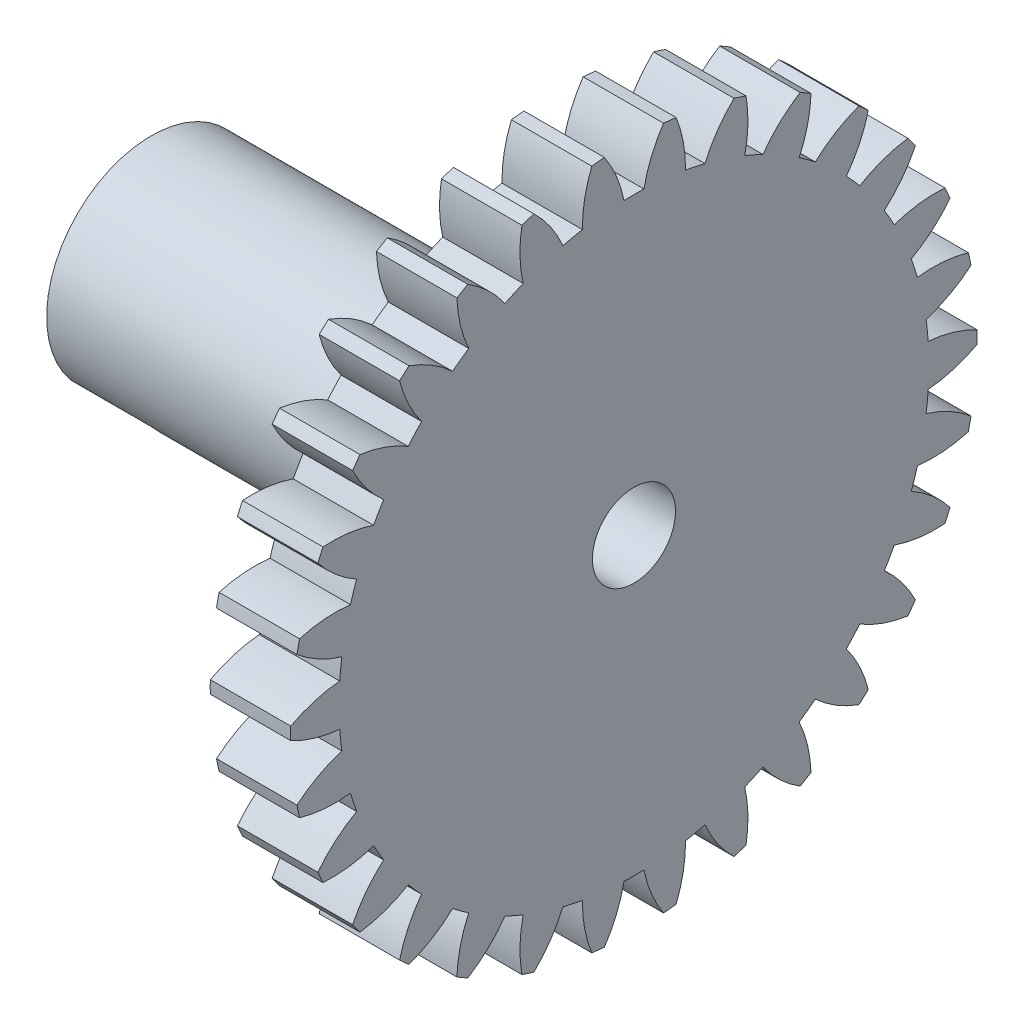
SolidWorks part; units mm, degrees
ref_plane "Plane1" through (0, 0, 0) normal (0, 0, 1) x (1, 0, 0)
ref_plane "Plane2" through (0, 0, 0) normal (0, 1, 0) x (1, 0, 0)
ref_plane "Plane3" through (0, 0, 0) normal (1, 0, 0) x (0, 0, -1)
other "Configuration Table"
sketch "HoldingSke" plane through (0, 0, 0) normal (0, 1, 0) x (1, 0, 0)
  line L0 (0, 0) -> (1.0825, -0.625)
  line L1 (-15, 0) -> (100, 0) construction
  line L2 (0, 0) -> (-2.1039, 2.3779)
  line L3 (0, 0) -> (-11.863, 4.5341)
  line L4 (0, 0) -> (7.479, 4.318)
  line L5 (0, 0) -> (-10.3065, -3.844)
  line L6 (0, 0) -> (-4.5593, -3.0762)
  line L7 (-2.1039, 2.3779) -> (0.2639, 13.1201)
  line L8 (-76.2, 54.61) -> (-76.1, 54.61)
  line L9 (-71.009, 38.7566) -> (-53.1078, 45.2721)
  line L10 (-76.2, 71.12) -> (104.1128, 71.12)
  line L11 (0, 0) -> (-5.5, 0)
  line L12 (-76.2, 101.6) -> (-76.17, 101.6)
  line L13 (24.9733, 27.94) -> (52.9518, 28.4284)
  line L14 (24.9733, 27.94) -> (24.9743, 27.94)
  line L15 (24.9733, 27.94) -> (100.4006, 29.5858)
  line L16 (-63.627, -0.8) -> (-12.827, -0.8)
  circle A0 centre (0, 0) radius 0.4
  circle A1 centre (0, 0) radius 1.9
  circle A2 centre (0, 0) radius 1.9
  circle A3 centre (0, 0) radius 0.4
  dimension "MHD" = 3.8
  dimension "Hub_dia" = 3.8
  dimension "Bore" = 0.8
  dimension "MBD" = 0.8
  dimension "Num_teeth" = 30
  dimension "Pitch" = 1.25
  dimension "Overall_len" = 11
  dimension "Show_teeth" = 30
  dimension "Thickness" = 5.5
  dimension "OAL" = 11.0001
  dimension "T_dim" = 0.1
  dimension "Ap" = 20
  dimension "H" = 19.05
  dimension "Pitch_radius" = 180.3128
  dimension "Width" = 5.5
  dimension "Backlash" = 0.03
  dimension "Addendum_fac" = 1
  dimension "Dedendum_fac" = 1.25
  dimension "Clearance_fac" = 0.25
  dimension "Dedendum_add" = 0.001
  dimension "Module" = 0.8
sketch "BasProSke" plane through (0, 0, 0) normal (0, 1, 0) x (1, 0, 0)
  line L0 (-10, 0) -> (60, 0) construction
  line L1 (0, 0) -> (0, 12.8)
  line L2 (0, 0) -> (5.5, 0)
  line L3 (5.5, 0) -> (5.5, 12.8)
  line L4 (5.5, 12.8) -> (0, 12.8)
  dimension "Thickness" = 5.5
  dimension "Diameter" = 25.6
revolve "Base-Revolve" add sketch "BasProSke" angle 360 about L0
sketch "TooCutSke" plane through (0, 0, 0) normal (1, 0, 0) x (0, 0, -1)
  line L1 (0, 0) -> (0, 107) construction
  line L2 (0, 0) -> (-0.6805, 11.9807) construction
  line L3 (0, 0) -> (-2.5058, 23.8411) construction
  line L4 (-0.6805, 11.9807) -> (-1.2529, 11.9205) construction
  arc A0 (0.3724, 10.9927) -> (-0.3724, 10.9927) centre (0, 0) ccw
  arc A1 (1.1205, 12.7764) -> (-1.1205, 12.7764) centre (0, 0) ccw
  circle A2 centre (0, 0) radius 12 construction
  circle A3 centre (0, 0) radius 11.2763 construction
  arc A4 (-0.3724, 10.9927) -> (-1.1205, 12.7764) centre (-5.0822, 10.0661) ccw
  arc A5 (1.1205, 12.7764) -> (0.3724, 10.9927) centre (5.0822, 10.0661) ccw
  dimension "Root_dia" = 21.998
  dimension "Overcut_dia" = 25.6508
  dimension "Pitch_dia" = 24
  dimension "Base_dia" = 22.5526
  dimension "Flank_rad" = 4.8
  dimension "Half_ang" = 6
  dimension "Half_CT" = 0.5755
extrude "ToothCut" cut sketch "TooCutSke" along normal through all
fillet "Breaks" [suppressed] radius 0.016
fillet "RootFillets" [suppressed] radius 0.201
pattern_circular "TeethCuts" count 30 over 360 about axis through (0, 0, 0) along (1, 0, 0) of "ToothCut", "RootFillets", "Breaks"
sketch "HubNeaOneSke" plane through (0, 0, 0) normal (-1, 0, 0) x (0, 0, 1)
  circle A0 centre (0, 0) radius 1.9
  dimension "Diameter" = 3.8
extrude "HubNearOne" add sketch "HubNeaOneSke" along normal blind 5.5001
sketch "HubNeaBotSke" plane through (0, 0, 0) normal (-1, 0, 0) x (0, 0, 1)
  circle A0 centre (0, 0) radius 1.9
  dimension "Diameter" = 3.8
extrude "HubNearBoth" [suppressed] add sketch "HubNeaBotSke" along normal blind 2.75
ref_plane "FarPln" through (5.5, 0, 0) normal (1, 0, 0) x (0, 0, -1)
sketch "HubFarSke" plane through (5.5, 0, 0) normal (1, 0, 0) x (0, 0, -1)
  circle A0 centre (0, 0) radius 1.9
  dimension "Diameter" = 3.8
extrude "HubFar" [suppressed] add sketch "HubFarSke" along normal blind 2.75
sketch "BorSke" plane through (0, 0, 0) normal (1, 0, 0) x (0, 0, -1)
  circle A0 centre (0, 0) radius 0.4
  dimension "Diameter" = 0.8
extrude "Bore" cut sketch "BorSke" along normal mid plane 22.0001
sketch "KeySke" plane through (0, 0, 0) normal (1, 0, 0) x (0, 0, -1)
  line L0 (-0.05, 0) -> (-0.05, 0.5)
  line L1 (-0.05, 0.5) -> (0.05, 0.5)
  line L2 (0.05, 0.5) -> (0.05, 0)
  line L3 (0, 0) -> (0, 34) construction
  line L4 (-0.05, 0) -> (0.05, 0)
  dimension "Offset" = 0.5
  dimension "Width" = 0.1
extrude "Keyway" [suppressed] cut sketch "KeySke" along normal mid plane 22.0001
pattern_circular "Keyway2" [suppressed] count 2 every 90 about axis through (-10, 0, 0) along (1, 0, 0)
sketch "Sketch1" plane through (0, 0, 0) normal (-1, 0, 0) x (0, 0, 1)
  circle A0 centre (0, 0) radius 3.9
  dimension "D1" = 7.8
extrude "Boss-Extrude1" add sketch "Sketch1" along normal blind 15
sketch "Sketch2" plane through (-15, 0, 0) normal (-1, 0, 0) x (0, 0, 1)
  circle A0 centre (0, 0) radius 1.55
  dimension "D1" = 3.1
extrude "Cut-Extrude1" cut sketch "Sketch2" against normal blind 28
sketch "Sketch3" plane through (-15, 0, 0) normal (-1, 0, 0) x (0, 0, 1)
  line L0 (-3, -2.492) -> (3, -2.492)
  circle A1 centre (0, 0) radius 3.9
  arc A2 (-3, -2.492) -> (3, -2.492) centre (0, 0) ccw
  dimension "D2" = 6
  dimension "D1" = 0
extrude "Cut-Extrude2" cut sketch "Sketch3" against normal blind 3
sketch "Sketch4" plane through (5.5, 0, 0) normal (1, 0, 0) x (0, 0, -1)
  arc A120 (-12.7978, -0.2349) -> (-10.9714, -0.7787) centre (-10.5422, 4.0021) ccw
  arc A121 (-10.9714, -0.7787) -> (-10.8935, -1.5194) centre (0, 0) ccw
  arc A122 (-10.8935, -1.5194) -> (-12.567, -2.4311) centre (-9.4798, -6.1065) ccw
  arc A123 (-12.567, -2.4311) -> (-12.4693, -2.8906) centre (0, 0) ccw
  arc A124 (-12.4693, -2.8906) -> (-10.5698, -3.0427) centre (-11.1439, 1.7228) ccw
  arc A125 (-10.5698, -3.0427) -> (-10.3396, -3.7511) centre (0, 0) ccw
  arc A126 (-10.3396, -3.7511) -> (-11.7869, -4.9908) centre (-8.003, -7.944) ccw
  arc A127 (-11.7869, -4.9908) -> (-11.5959, -5.4199) centre (0, 0) ccw
  arc A128 (-11.5959, -5.4199) -> (-9.7062, -5.1738) centre (-11.2586, -0.6318) ccw
  arc A129 (-9.7062, -5.1738) -> (-9.3337, -5.8189) centre (0, 0) ccw
  arc A130 (-9.3337, -5.8189) -> (-10.4917, -7.3324) centre (-6.1764, -9.4343) ccw
  arc A131 (-10.4917, -7.3324) -> (-10.2156, -7.7124) centre (0, 0) ccw
  arc A132 (-10.2156, -7.7124) -> (-8.4184, -7.0788) centre (-10.8812, -2.9588) ccw
  arc A133 (-8.4184, -7.0788) -> (-7.92, -7.6323) centre (0, 0) ccw
  arc A134 (-7.92, -7.6323) -> (-8.738, -9.3535) centre (-4.08, -10.5123) ccw
  arc A135 (-8.738, -9.3535) -> (-8.3889, -9.6678) centre (0, 0) ccw
  arc A136 (-8.3889, -9.6678) -> (-6.7627, -8.6744) centre (-10.0283, -5.1564) ccw
  arc A137 (-6.7627, -8.6744) -> (-6.16, -9.1122) centre (0, 0) ccw
  arc A138 (-6.16, -9.1122) -> (-6.6023, -10.9658) centre (-1.8052, -11.1309) ccw
  arc A139 (-6.6023, -10.9658) -> (-6.1955, -11.2007) centre (0, 0) ccw
  arc A140 (-6.1955, -11.2007) -> (-4.8114, -9.8908) centre (-8.737, -7.1288) ccw
  arc A141 (-4.8114, -9.8908) -> (-4.1309, -10.1938) centre (0, 0) ccw
  arc A142 (-4.1309, -10.1938) -> (-4.1781, -12.0989) centre (0.5485, -11.263) ccw
  arc A143 (-4.1781, -12.0989) -> (-3.7314, -12.2441) centre (0, 0) ccw
  arc A144 (-3.7314, -12.2441) -> (-2.6498, -10.675) centre (-7.064, -8.7895) ccw
  arc A145 (-2.6498, -10.675) -> (-1.9212, -10.8299) centre (0, 0) ccw
  arc A146 (-1.9212, -10.8299) -> (-1.5713, -12.7032) centre (2.8782, -10.9028) ccw
  arc A147 (-1.5713, -12.7032) -> (-1.1042, -12.7523) centre (0, 0) ccw
  arc A148 (-1.1042, -12.7523) -> (-0.3724, -10.9927) centre (-5.0822, -10.0661) ccw
  arc A149 (-0.3724, -10.9927) -> (0.3724, -10.9927) centre (0, 0) ccw
  arc A150 (0.3724, -10.9927) -> (1.1042, -12.7523) centre (5.0822, -10.0661) ccw
  arc A151 (1.1042, -12.7523) -> (1.5713, -12.7032) centre (0, 0) ccw
  arc A152 (1.5713, -12.7032) -> (1.9212, -10.8299) centre (-2.8782, -10.9028) ccw
  arc A153 (1.9212, -10.8299) -> (2.6498, -10.675) centre (0, 0) ccw
  arc A154 (2.6498, -10.675) -> (3.7314, -12.2441) centre (7.064, -8.7895) ccw
  arc A155 (3.7314, -12.2441) -> (4.1781, -12.0989) centre (0, 0) ccw
  arc A156 (4.1781, -12.0989) -> (4.1309, -10.1938) centre (-0.5485, -11.263) ccw
  arc A157 (4.1309, -10.1938) -> (4.8114, -9.8908) centre (0, 0) ccw
  arc A158 (4.8114, -9.8908) -> (6.1955, -11.2007) centre (8.737, -7.1288) ccw
  arc A159 (6.1955, -11.2007) -> (6.6023, -10.9658) centre (0, 0) ccw
  arc A160 (6.6023, -10.9658) -> (6.16, -9.1122) centre (1.8052, -11.1309) ccw
  arc A161 (6.16, -9.1122) -> (6.7627, -8.6744) centre (0, 0) ccw
  arc A162 (6.7627, -8.6744) -> (8.3889, -9.6678) centre (10.0283, -5.1564) ccw
  arc A163 (8.3889, -9.6678) -> (8.738, -9.3535) centre (0, 0) ccw
  arc A164 (8.738, -9.3535) -> (7.92, -7.6323) centre (4.08, -10.5123) ccw
  arc A165 (7.92, -7.6323) -> (8.4184, -7.0788) centre (0, 0) ccw
  arc A166 (8.4184, -7.0788) -> (10.2156, -7.7124) centre (10.8812, -2.9588) ccw
  arc A167 (10.2156, -7.7124) -> (10.4917, -7.3324) centre (0, 0) ccw
  arc A168 (10.4917, -7.3324) -> (9.3337, -5.8189) centre (6.1764, -9.4343) ccw
  arc A169 (9.3337, -5.8189) -> (9.7062, -5.1738) centre (0, 0) ccw
  arc A170 (9.7062, -5.1738) -> (11.5959, -5.4199) centre (11.2586, -0.6318) ccw
  arc A171 (11.5959, -5.4199) -> (11.7869, -4.9908) centre (0, 0) ccw
  arc A172 (11.7869, -4.9908) -> (10.3396, -3.7511) centre (8.003, -7.944) ccw
  arc A173 (10.3396, -3.7511) -> (10.5698, -3.0427) centre (0, 0) ccw
  arc A174 (10.5698, -3.0427) -> (12.4693, -2.8906) centre (11.1439, 1.7228) ccw
  arc A175 (12.4693, -2.8906) -> (12.567, -2.4311) centre (0, 0) ccw
  arc A176 (12.567, -2.4311) -> (10.8935, -1.5194) centre (9.4798, -6.1065) ccw
  arc A177 (10.8935, -1.5194) -> (10.9714, -0.7787) centre (0, 0) ccw
  arc A178 (10.9714, -0.7787) -> (12.7978, -0.2349) centre (10.5422, 4.0021) ccw
  arc A179 (12.7978, -0.2349) -> (12.7978, 0.2349) centre (0, 0) ccw
  arc A180 (12.7978, 0.2349) -> (10.9714, 0.7787) centre (10.5422, -4.0021) ccw
  arc A181 (10.9714, 0.7787) -> (10.8935, 1.5194) centre (0, 0) ccw
  arc A182 (10.8935, 1.5194) -> (12.567, 2.4311) centre (9.4798, 6.1065) ccw
  arc A183 (12.567, 2.4311) -> (12.4693, 2.8906) centre (0, 0) ccw
  arc A184 (12.4693, 2.8906) -> (10.5698, 3.0427) centre (11.1439, -1.7228) ccw
  arc A185 (10.5698, 3.0427) -> (10.3396, 3.7511) centre (0, 0) ccw
  arc A186 (10.3396, 3.7511) -> (11.7869, 4.9908) centre (8.003, 7.944) ccw
  arc A187 (11.7869, 4.9908) -> (11.5959, 5.4199) centre (0, 0) ccw
  arc A188 (11.5959, 5.4199) -> (9.7062, 5.1738) centre (11.2586, 0.6318) ccw
  arc A189 (9.7062, 5.1738) -> (9.3337, 5.8189) centre (0, 0) ccw
  arc A190 (9.3337, 5.8189) -> (10.4917, 7.3324) centre (6.1764, 9.4343) ccw
  arc A191 (10.4917, 7.3324) -> (10.2156, 7.7124) centre (0, 0) ccw
  arc A192 (10.2156, 7.7124) -> (8.4184, 7.0788) centre (10.8812, 2.9588) ccw
  arc A193 (8.4184, 7.0788) -> (7.92, 7.6323) centre (0, 0) ccw
  arc A194 (7.92, 7.6323) -> (8.738, 9.3535) centre (4.08, 10.5123) ccw
  arc A195 (8.738, 9.3535) -> (8.3889, 9.6678) centre (0, 0) ccw
  arc A196 (8.3889, 9.6678) -> (6.7627, 8.6744) centre (10.0283, 5.1564) ccw
  arc A197 (6.7627, 8.6744) -> (6.16, 9.1122) centre (0, 0) ccw
  arc A198 (6.16, 9.1122) -> (6.6023, 10.9658) centre (1.8052, 11.1309) ccw
  arc A199 (6.6023, 10.9658) -> (6.1955, 11.2007) centre (0, 0) ccw
  arc A200 (6.1955, 11.2007) -> (4.8114, 9.8908) centre (8.737, 7.1288) ccw
  arc A201 (4.8114, 9.8908) -> (4.1309, 10.1938) centre (0, 0) ccw
  arc A202 (4.1309, 10.1938) -> (4.1781, 12.0989) centre (-0.5485, 11.263) ccw
  arc A203 (4.1781, 12.0989) -> (3.7314, 12.2441) centre (0, 0) ccw
  arc A204 (3.7314, 12.2441) -> (2.6498, 10.675) centre (7.064, 8.7895) ccw
  arc A205 (2.6498, 10.675) -> (1.9212, 10.8299) centre (0, 0) ccw
  arc A206 (1.9212, 10.8299) -> (1.5713, 12.7032) centre (-2.8782, 10.9028) ccw
  arc A207 (1.5713, 12.7032) -> (1.1042, 12.7523) centre (0, 0) ccw
  arc A208 (1.1042, 12.7523) -> (0.3724, 10.9927) centre (5.0822, 10.0661) ccw
  arc A209 (0.3724, 10.9927) -> (-0.3724, 10.9927) centre (0, 0) ccw
  arc A210 (-0.3724, 10.9927) -> (-1.1042, 12.7523) centre (-5.0822, 10.0661) ccw
  arc A211 (-1.1042, 12.7523) -> (-1.5713, 12.7032) centre (0, 0) ccw
  arc A212 (-1.5713, 12.7032) -> (-1.9212, 10.8299) centre (2.8782, 10.9028) ccw
  arc A213 (-1.9212, 10.8299) -> (-2.6498, 10.675) centre (0, 0) ccw
  arc A214 (-2.6498, 10.675) -> (-3.7314, 12.2441) centre (-7.064, 8.7895) ccw
  arc A215 (-3.7314, 12.2441) -> (-4.1781, 12.0989) centre (0, 0) ccw
  arc A216 (-4.1781, 12.0989) -> (-4.1309, 10.1938) centre (0.5485, 11.263) ccw
  arc A217 (-4.1309, 10.1938) -> (-4.8114, 9.8908) centre (0, 0) ccw
  arc A218 (-4.8114, 9.8908) -> (-6.1955, 11.2007) centre (-8.737, 7.1288) ccw
  arc A219 (-6.1955, 11.2007) -> (-6.6023, 10.9658) centre (0, 0) ccw
  arc A220 (-6.6023, 10.9658) -> (-6.16, 9.1122) centre (-1.8052, 11.1309) ccw
  arc A221 (-6.16, 9.1122) -> (-6.7627, 8.6744) centre (0, 0) ccw
  arc A222 (-6.7627, 8.6744) -> (-8.3889, 9.6678) centre (-10.0283, 5.1564) ccw
  arc A223 (-8.3889, 9.6678) -> (-8.738, 9.3535) centre (0, 0) ccw
  arc A224 (-8.738, 9.3535) -> (-7.92, 7.6323) centre (-4.08, 10.5123) ccw
  arc A225 (-7.92, 7.6323) -> (-8.4184, 7.0788) centre (0, 0) ccw
  arc A226 (-8.4184, 7.0788) -> (-10.2156, 7.7124) centre (-10.8812, 2.9588) ccw
  arc A227 (-10.2156, 7.7124) -> (-10.4917, 7.3324) centre (0, 0) ccw
  arc A228 (-10.4917, 7.3324) -> (-9.3337, 5.8189) centre (-6.1764, 9.4343) ccw
  arc A229 (-9.3337, 5.8189) -> (-9.7062, 5.1738) centre (0, 0) ccw
  arc A230 (-9.7062, 5.1738) -> (-11.5959, 5.4199) centre (-11.2586, 0.6318) ccw
  arc A231 (-11.5959, 5.4199) -> (-11.7869, 4.9908) centre (0, 0) ccw
  arc A232 (-11.7869, 4.9908) -> (-10.3396, 3.7511) centre (-8.003, 7.944) ccw
  arc A233 (-10.3396, 3.7511) -> (-10.5698, 3.0427) centre (0, 0) ccw
  arc A234 (-10.5698, 3.0427) -> (-12.4693, 2.8906) centre (-11.1439, -1.7228) ccw
  arc A235 (-12.4693, 2.8906) -> (-12.567, 2.4311) centre (0, 0) ccw
  arc A236 (-12.567, 2.4311) -> (-10.8935, 1.5194) centre (-9.4798, 6.1065) ccw
  arc A237 (-10.8935, 1.5194) -> (-10.9714, 0.7787) centre (0, 0) ccw
  arc A238 (-10.9714, 0.7787) -> (-12.7978, 0.2349) centre (-10.5422, -4.0021) ccw
  arc A239 (-12.7978, 0.2349) -> (-12.7978, -0.2349) centre (0, 0) ccw
  arc A240 (-12.7978, -0.2349) -> (-10.9714, -0.7787) centre (-10.5422, 4.0021) ccw
  arc A241 (-10.9714, -0.7787) -> (-10.8935, -1.5194) centre (0, 0) ccw
  arc A242 (-10.8935, -1.5194) -> (-12.567, -2.4311) centre (-9.4798, -6.1065) ccw
  arc A243 (-12.567, -2.4311) -> (-12.4693, -2.8906) centre (0, 0) ccw
  arc A244 (-12.4693, -2.8906) -> (-10.5698, -3.0427) centre (-11.1439, 1.7228) ccw
  arc A245 (-10.5698, -3.0427) -> (-10.3396, -3.7511) centre (0, 0) ccw
  arc A246 (-10.3396, -3.7511) -> (-11.7869, -4.9908) centre (-8.003, -7.944) ccw
  arc A247 (-11.7869, -4.9908) -> (-11.5959, -5.4199) centre (0, 0) ccw
  arc A248 (-11.5959, -5.4199) -> (-9.7062, -5.1738) centre (-11.2586, -0.6318) ccw
  arc A249 (-9.7062, -5.1738) -> (-9.3337, -5.8189) centre (0, 0) ccw
  arc A250 (-9.3337, -5.8189) -> (-10.4917, -7.3324) centre (-6.1764, -9.4343) ccw
  arc A251 (-10.4917, -7.3324) -> (-10.2156, -7.7124) centre (0, 0) ccw
  arc A252 (-10.2156, -7.7124) -> (-8.4184, -7.0788) centre (-10.8812, -2.9588) ccw
  arc A253 (-8.4184, -7.0788) -> (-7.92, -7.6323) centre (0, 0) ccw
  arc A254 (-7.92, -7.6323) -> (-8.738, -9.3535) centre (-4.08, -10.5123) ccw
  arc A255 (-8.738, -9.3535) -> (-8.3889, -9.6678) centre (0, 0) ccw
  arc A256 (-8.3889, -9.6678) -> (-6.7627, -8.6744) centre (-10.0283, -5.1564) ccw
  arc A257 (-6.7627, -8.6744) -> (-6.16, -9.1122) centre (0, 0) ccw
  arc A258 (-6.16, -9.1122) -> (-6.6023, -10.9658) centre (-1.8052, -11.1309) ccw
  arc A259 (-6.6023, -10.9658) -> (-6.1955, -11.2007) centre (0, 0) ccw
  arc A260 (-6.1955, -11.2007) -> (-4.8114, -9.8908) centre (-8.737, -7.1288) ccw
  arc A261 (-4.8114, -9.8908) -> (-4.1309, -10.1938) centre (0, 0) ccw
  arc A262 (-4.1309, -10.1938) -> (-4.1781, -12.0989) centre (0.5485, -11.263) ccw
  arc A263 (-4.1781, -12.0989) -> (-3.7314, -12.2441) centre (0, 0) ccw
  arc A264 (-3.7314, -12.2441) -> (-2.6498, -10.675) centre (-7.064, -8.7895) ccw
  arc A265 (-2.6498, -10.675) -> (-1.9212, -10.8299) centre (0, 0) ccw
  arc A266 (-1.9212, -10.8299) -> (-1.5713, -12.7032) centre (2.8782, -10.9028) ccw
  arc A267 (-1.5713, -12.7032) -> (-1.1042, -12.7523) centre (0, 0) ccw
  arc A268 (-1.1042, -12.7523) -> (-0.3724, -10.9927) centre (-5.0822, -10.0661) ccw
  arc A269 (-0.3724, -10.9927) -> (0.3724, -10.9927) centre (0, 0) ccw
  arc A270 (0.3724, -10.9927) -> (1.1042, -12.7523) centre (5.0822, -10.0661) ccw
  arc A271 (1.1042, -12.7523) -> (1.5713, -12.7032) centre (0, 0) ccw
  arc A272 (1.5713, -12.7032) -> (1.9212, -10.8299) centre (-2.8782, -10.9028) ccw
  arc A273 (1.9212, -10.8299) -> (2.6498, -10.675) centre (0, 0) ccw
  arc A274 (2.6498, -10.675) -> (3.7314, -12.2441) centre (7.064, -8.7895) ccw
  arc A275 (3.7314, -12.2441) -> (4.1781, -12.0989) centre (0, 0) ccw
  arc A276 (4.1781, -12.0989) -> (4.1309, -10.1938) centre (-0.5485, -11.263) ccw
  arc A277 (4.1309, -10.1938) -> (4.8114, -9.8908) centre (0, 0) ccw
  arc A278 (4.8114, -9.8908) -> (6.1955, -11.2007) centre (8.737, -7.1288) ccw
  arc A279 (6.1955, -11.2007) -> (6.6023, -10.9658) centre (0, 0) ccw
  arc A280 (6.6023, -10.9658) -> (6.16, -9.1122) centre (1.8052, -11.1309) ccw
  arc A281 (6.16, -9.1122) -> (6.7627, -8.6744) centre (0, 0) ccw
  arc A282 (6.7627, -8.6744) -> (8.3889, -9.6678) centre (10.0283, -5.1564) ccw
  arc A283 (8.3889, -9.6678) -> (8.738, -9.3535) centre (0, 0) ccw
  arc A284 (8.738, -9.3535) -> (7.92, -7.6323) centre (4.08, -10.5123) ccw
  arc A285 (7.92, -7.6323) -> (8.4184, -7.0788) centre (0, 0) ccw
  arc A286 (8.4184, -7.0788) -> (10.2156, -7.7124) centre (10.8812, -2.9588) ccw
  arc A287 (10.2156, -7.7124) -> (10.4917, -7.3324) centre (0, 0) ccw
  arc A288 (10.4917, -7.3324) -> (9.3337, -5.8189) centre (6.1764, -9.4343) ccw
  arc A289 (9.3337, -5.8189) -> (9.7062, -5.1738) centre (0, 0) ccw
  arc A290 (9.7062, -5.1738) -> (11.5959, -5.4199) centre (11.2586, -0.6318) ccw
  arc A291 (11.5959, -5.4199) -> (11.7869, -4.9908) centre (0, 0) ccw
  arc A292 (11.7869, -4.9908) -> (10.3396, -3.7511) centre (8.003, -7.944) ccw
  arc A293 (10.3396, -3.7511) -> (10.5698, -3.0427) centre (0, 0) ccw
  arc A294 (10.5698, -3.0427) -> (12.4693, -2.8906) centre (11.1439, 1.7228) ccw
  arc A295 (12.4693, -2.8906) -> (12.567, -2.4311) centre (0, 0) ccw
  arc A296 (12.567, -2.4311) -> (10.8935, -1.5194) centre (9.4798, -6.1065) ccw
  arc A297 (10.8935, -1.5194) -> (10.9714, -0.7787) centre (0, 0) ccw
  arc A298 (10.9714, -0.7787) -> (12.7978, -0.2349) centre (10.5422, 4.0021) ccw
  arc A299 (12.7978, -0.2349) -> (12.7978, 0.2349) centre (0, 0) ccw
  arc A300 (12.7978, 0.2349) -> (10.9714, 0.7787) centre (10.5422, -4.0021) ccw
  arc A301 (10.9714, 0.7787) -> (10.8935, 1.5194) centre (0, 0) ccw
  arc A302 (10.8935, 1.5194) -> (12.567, 2.4311) centre (9.4798, 6.1065) ccw
  arc A303 (12.567, 2.4311) -> (12.4693, 2.8906) centre (0, 0) ccw
  arc A304 (12.4693, 2.8906) -> (10.5698, 3.0427) centre (11.1439, -1.7228) ccw
  arc A305 (10.5698, 3.0427) -> (10.3396, 3.7511) centre (0, 0) ccw
  arc A306 (10.3396, 3.7511) -> (11.7869, 4.9908) centre (8.003, 7.944) ccw
  arc A307 (11.7869, 4.9908) -> (11.5959, 5.4199) centre (0, 0) ccw
  arc A308 (11.5959, 5.4199) -> (9.7062, 5.1738) centre (11.2586, 0.6318) ccw
  arc A309 (9.7062, 5.1738) -> (9.3337, 5.8189) centre (0, 0) ccw
  arc A310 (9.3337, 5.8189) -> (10.4917, 7.3324) centre (6.1764, 9.4343) ccw
  arc A311 (10.4917, 7.3324) -> (10.2156, 7.7124) centre (0, 0) ccw
  arc A312 (10.2156, 7.7124) -> (8.4184, 7.0788) centre (10.8812, 2.9588) ccw
  arc A313 (8.4184, 7.0788) -> (7.92, 7.6323) centre (0, 0) ccw
  arc A314 (7.92, 7.6323) -> (8.738, 9.3535) centre (4.08, 10.5123) ccw
  arc A315 (8.738, 9.3535) -> (8.3889, 9.6678) centre (0, 0) ccw
  arc A316 (8.3889, 9.6678) -> (6.7627, 8.6744) centre (10.0283, 5.1564) ccw
  arc A317 (6.7627, 8.6744) -> (6.16, 9.1122) centre (0, 0) ccw
  arc A318 (6.16, 9.1122) -> (6.6023, 10.9658) centre (1.8052, 11.1309) ccw
  arc A319 (6.6023, 10.9658) -> (6.1955, 11.2007) centre (0, 0) ccw
  arc A320 (6.1955, 11.2007) -> (4.8114, 9.8908) centre (8.737, 7.1288) ccw
  arc A321 (4.8114, 9.8908) -> (4.1309, 10.1938) centre (0, 0) ccw
  arc A322 (4.1309, 10.1938) -> (4.1781, 12.0989) centre (-0.5485, 11.263) ccw
  arc A323 (4.1781, 12.0989) -> (3.7314, 12.2441) centre (0, 0) ccw
  arc A324 (3.7314, 12.2441) -> (2.6498, 10.675) centre (7.064, 8.7895) ccw
  arc A325 (2.6498, 10.675) -> (1.9212, 10.8299) centre (0, 0) ccw
  arc A326 (1.9212, 10.8299) -> (1.5713, 12.7032) centre (-2.8782, 10.9028) ccw
  arc A327 (1.5713, 12.7032) -> (1.1042, 12.7523) centre (0, 0) ccw
  arc A328 (1.1042, 12.7523) -> (0.3724, 10.9927) centre (5.0822, 10.0661) ccw
  arc A329 (0.3724, 10.9927) -> (-0.3724, 10.9927) centre (0, 0) ccw
  arc A330 (-0.3724, 10.9927) -> (-1.1042, 12.7523) centre (-5.0822, 10.0661) ccw
  arc A331 (-1.1042, 12.7523) -> (-1.5713, 12.7032) centre (0, 0) ccw
  arc A332 (-1.5713, 12.7032) -> (-1.9212, 10.8299) centre (2.8782, 10.9028) ccw
  arc A333 (-1.9212, 10.8299) -> (-2.6498, 10.675) centre (0, 0) ccw
  arc A334 (-2.6498, 10.675) -> (-3.7314, 12.2441) centre (-7.064, 8.7895) ccw
  arc A335 (-3.7314, 12.2441) -> (-4.1781, 12.0989) centre (0, 0) ccw
  arc A336 (-4.1781, 12.0989) -> (-4.1309, 10.1938) centre (0.5485, 11.263) ccw
  arc A337 (-4.1309, 10.1938) -> (-4.8114, 9.8908) centre (0, 0) ccw
  arc A338 (-4.8114, 9.8908) -> (-6.1955, 11.2007) centre (-8.737, 7.1288) ccw
  arc A339 (-6.1955, 11.2007) -> (-6.6023, 10.9658) centre (0, 0) ccw
  arc A340 (-6.6023, 10.9658) -> (-6.16, 9.1122) centre (-1.8052, 11.1309) ccw
  arc A341 (-6.16, 9.1122) -> (-6.7627, 8.6744) centre (0, 0) ccw
  arc A342 (-6.7627, 8.6744) -> (-8.3889, 9.6678) centre (-10.0283, 5.1564) ccw
  arc A343 (-8.3889, 9.6678) -> (-8.738, 9.3535) centre (0, 0) ccw
  arc A344 (-8.738, 9.3535) -> (-7.92, 7.6323) centre (-4.08, 10.5123) ccw
  arc A345 (-7.92, 7.6323) -> (-8.4184, 7.0788) centre (0, 0) ccw
  arc A346 (-8.4184, 7.0788) -> (-10.2156, 7.7124) centre (-10.8812, 2.9588) ccw
  arc A347 (-10.2156, 7.7124) -> (-10.4917, 7.3324) centre (0, 0) ccw
  arc A348 (-10.4917, 7.3324) -> (-9.3337, 5.8189) centre (-6.1764, 9.4343) ccw
  arc A349 (-9.3337, 5.8189) -> (-9.7062, 5.1738) centre (0, 0) ccw
  arc A350 (-9.7062, 5.1738) -> (-11.5959, 5.4199) centre (-11.2586, 0.6318) ccw
  arc A351 (-11.5959, 5.4199) -> (-11.7869, 4.9908) centre (0, 0) ccw
  arc A352 (-11.7869, 4.9908) -> (-10.3396, 3.7511) centre (-8.003, 7.944) ccw
  arc A353 (-10.3396, 3.7511) -> (-10.5698, 3.0427) centre (0, 0) ccw
  arc A354 (-10.5698, 3.0427) -> (-12.4693, 2.8906) centre (-11.1439, -1.7228) ccw
  arc A355 (-12.4693, 2.8906) -> (-12.567, 2.4311) centre (0, 0) ccw
  arc A356 (-12.567, 2.4311) -> (-10.8935, 1.5194) centre (-9.4798, 6.1065) ccw
  arc A357 (-10.8935, 1.5194) -> (-10.9714, 0.7787) centre (0, 0) ccw
  arc A358 (-10.9714, 0.7787) -> (-12.7978, 0.2349) centre (-10.5422, -4.0021) ccw
  arc A359 (-12.7978, 0.2349) -> (-12.7978, -0.2349) centre (0, 0) ccw
  dimension "D1" = 0
extrude "Cut-Extrude3" cut sketch "Sketch4" against normal blind 2.5
equation "' \"Module@HoldingSke\" = 6.35"
equation "' \"Num_teeth@HoldingSke\" = 12"
equation "' \"Ap@HoldingSke\" =  20"
equation "' \"Ap@HoldingSke\" = 20"
equation "' \"Width@HoldingSke\" = 0.5 * 25.4"
equation "' \"Hub_dia@HoldingSke\"= 1 * 25.4"
equation "' \"Hub_dia@HoldingSke\" = 1 * 25.4"
equation "' \"Overall_len@HoldingSke\" = 1.0 * 25.4"
equation "' \"Bore@HoldingSke\" = 0.75 * 25.4"
equation "' \"T_dim@HoldingSke\" = 0.1 * 25.4"
equation "' \"Width@KeySke\" = 0.25 * 25.4"
equation "' \"Show_teeth@HoldingSke\" = 13"
equation "' \"Backlash@HoldingSke\" = 0.009 * 25.4"
equation "' \"Addendum_fac@HoldingSke\" = 1.0"
equation "' \"Dedendum_fac@HoldingSke\" = 1.25"
equation "' \"Dedendum_add@HoldingSke\" = 0.00005 * 25.4"
equation "' \"Clearance_fac@HoldingSke\" = 0.25"
equation "\"Pitch@HoldingSke\" = 1 / \"Module@HoldingSke\""
equation "\"Overcut_dia@TooCutSke\" = (\"Num_teeth@HoldingSke\" + 2 * \"Addendum_fac@HoldingSke\") / \"Pitch@HoldingSke\" + 0.002 * 25.4"
equation "\"Pitch_dia@TooCutSke\" = \"Num_teeth@HoldingSke\" / \"Pitch@HoldingSke\""
equation "\"Base_dia@TooCutSke\" = \"Num_teeth@HoldingSke\" / \"Pitch@HoldingSke\" * cos((\"Ap@HoldingSke\"  * 3.14159265 / 180))"
equation "\"Root_dia@TooCutSke\" = (\"Num_teeth@HoldingSke\" + 2) / \"Pitch@HoldingSke\" - 2 * (\"Addendum_fac@HoldingSke\" + \"Dedendum_fac@HoldingSke\") / \"Pitch@HoldingSke\" - \"Dedendum_add@HoldingSke\" * 2"
equation "\"Half_ang@TooCutSke\" = 180 / \"Num_teeth@HoldingSke\""
equation "\"Half_CT@TooCutSke\" = \"Num_teeth@HoldingSke\" / \"Pitch@HoldingSke\" * sin((3.14159265 / 2 / \"Num_teeth@HoldingSke\")) / 2 - 7 * \"Backlash@HoldingSke\" / 4"
equation "\"Flank_rad@TooCutSke\" = \"Num_teeth@HoldingSke\" / \"Pitch@HoldingSke\" / 5"
equation "\"Radius@RootFillets\" = \"Clearance_fac@HoldingSke\" / \"Pitch@HoldingSke\" + \"Dedendum_add@HoldingSke\""
equation "\"Break_rad@Breaks\" = 0.02 / \"Pitch@HoldingSke\""
equation "\"Thickness@HoldingSke\" = \"Width@HoldingSke\""
equation "\"OAL@HoldingSke\" = \"Thickness@HoldingSke\""
equation "\"MHD@HoldingSke\" = (\"Num_teeth@HoldingSke\" + 2) / \"Pitch@HoldingSke\" - 2 * (\"Addendum_fac@HoldingSke\" + \"Dedendum_fac@HoldingSke\")  / \"Pitch@HoldingSke\" - \"Dedendum_add@HoldingSke\" * 2"
equation "\"MBD@HoldingSke\" = (\"Num_teeth@HoldingSke\" + 2) / \"Pitch@HoldingSke\" - 2 * (\"Addendum_fac@HoldingSke\" + \"Dedendum_fac@HoldingSke\")  / \"Pitch@HoldingSke\" - \"Dedendum_add@HoldingSke\" * 2 - 0.002 * 25.4"
equation "\"MHD@HoldingSke\" = ((sgn( \"MHD@HoldingSke\" - \"Hub_dia@HoldingSke\" )-1)*( \"MHD@HoldingSke\" - \"Hub_dia@HoldingSke\" ))/-2+ \"Hub_dia@HoldingSke\""
equation "\"MBD@HoldingSke\" = ((sgn( \"MBD@HoldingSke\" - \"Bore@HoldingSke\" )-1)*( \"MBD@HoldingSke\" - \"Bore@HoldingSke\" ))/-2+ \"Bore@HoldingSke\""
equation "\"OAL@HoldingSke\" = ((sgn( \"OAL@HoldingSke\" - \"Overall_len@HoldingSke\" )+1)*( \"OAL@HoldingSke\" - \"Overall_len@HoldingSke\" ))/2 + \"Overall_len@HoldingSke\" + 0.000002 * 25.4"
equation "\"Num_teeth@TeethCuts\" = int( \"Show_teeth@HoldingSke\" ) + 1"
equation "\"Num_teeth@TeethCuts\" = ((sgn( \"Num_teeth@TeethCuts\" - \"Num_teeth@HoldingSke\" )-1)*( \"Num_teeth@TeethCuts\" - \"Num_teeth@HoldingSke\" ))/-2+ \"Num_teeth@HoldingSke\""
equation "\"Num_teeth@TeethCuts\" = ((sgn( \"Num_teeth@TeethCuts\" - 2.0)+1)*( \"Num_teeth@TeethCuts\" - 2.0))/2 +2.0"
equation "\"Angle@TeethCuts\" = 360.0 / \"Num_teeth@HoldingSke\""
equation "\"Diameter@BasProSke\" = (\"Num_teeth@HoldingSke\" + 2 * \"Addendum_fac@HoldingSke\") / \"Pitch@HoldingSke\""
equation "\"Thickness@BasProSke\"  = \"Thickness@HoldingSke\""
equation "' \"Fillet_rad@BasProSke\" =  \"Thickness@HoldingSke\" * 0.05"
equation "' \"Fillet_rad@BasProSke\" = \"Thickness@HoldingSke\" * 0.05"
equation "\"MHD@HoldingSke\" = ((sgn( \"MHD@HoldingSke\" - \"Root_dia@TooCutSke\" )-1)*( \"MHD@HoldingSke\" - \"Root_dia@TooCutSke\" ))/-2+ \"Root_dia@TooCutSke\""
equation "\"Diameter@HubNeaOneSke\" = \"MHD@HoldingSke\""
equation "\"Length@HubNearOne\" = \"OAL@HoldingSke\" - \"Thickness@BasProSke\""
equation "\"Diameter@HubNeaBotSke\" = \"MHD@HoldingSke\""
equation "\"Length@HubNearBoth\" = ( \"OAL@HoldingSke\" - \"Thickness@BasProSke\" ) / 2.0"
equation "\"Thickness@FarPln\" = \"Thickness@BasProSke\""
equation "\"Diameter@HubFarSke\" = \"MHD@HoldingSke\""
equation "\"Length@HubFar\" = ( \"OAL@HoldingSke\" - \"Thickness@BasProSke\" ) / 2.0"
equation "\"Diameter@BorSke\" = \"MBD@HoldingSke\""
equation "\"D1@Bore\" = \"OAL@HoldingSke\" * 2.0"
equation "\"D1@Keyway\" = \"OAL@HoldingSke\" * 2.0"
equation "\"Offset@KeySke\" = \"T_dim@HoldingSke\" + \"MBD@HoldingSke\" / 2.0"
